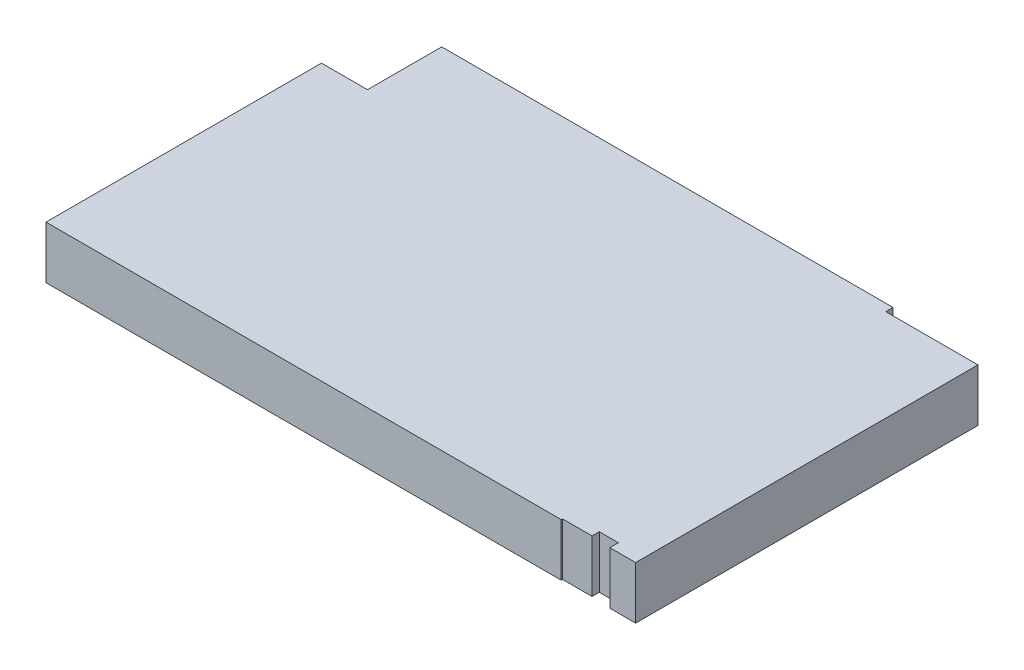
SolidWorks part; units mm, degrees
ref_plane "Front Plane" through (0, 0, 0) normal (0, 0, 1) x (1, 0, 0)
ref_plane "Top Plane" through (0, 0, 0) normal (0, 1, 0) x (1, 0, 0)
ref_plane "Right Plane" through (0, 0, 0) normal (1, 0, 0) x (0, 0, -1)
sketch "Sketch1" plane through (0, 0, 0) normal (0, 1, 0) x (1, 0, 0)
  line L0 (0, 0) -> (0, 75.95)
  line L1 (0, 75.95) -> (12.7, 75.95)
  line L2 (12.7, 75.95) -> (12.7, 96.4)
  line L3 (12.7, 96.4) -> (137.15, 96.4)
  line L4 (137.15, 96.4) -> (137.15, 94.4)
  line L5 (137.15, 94.4) -> (162.57, 94.4)
  line L6 (162.57, 94.4) -> (162.57, 0)
  line L7 (162.57, 0) -> (155.45, 0)
  line L8 (155.45, 0) -> (155.45, 2.35)
  line L9 (155.45, 2.35) -> (150.2, 2.35)
  line L10 (150.2, 2.35) -> (150.2, 0.35)
  line L11 (150.2, 0.35) -> (142.05, 0.35)
  line L12 (142.05, 0.35) -> (142.05, 0)
  line L13 (142.05, 0) -> (0, 0)
  dimension "D1" = 2
  dimension "D2" = 162.57
  dimension "D3" = 2.35
  dimension "D4" = 5.25
  dimension "D5" = 13.4
  dimension "D6" = 0.35
  dimension "D7" = 142.05
  dimension "D8" = 75.95
  dimension "D9" = 12.7
  dimension "D10" = 137.15
  dimension "D11" = 96.4
extrude "Boss-Extrude1" add sketch "Sketch1" along normal blind 14.47
